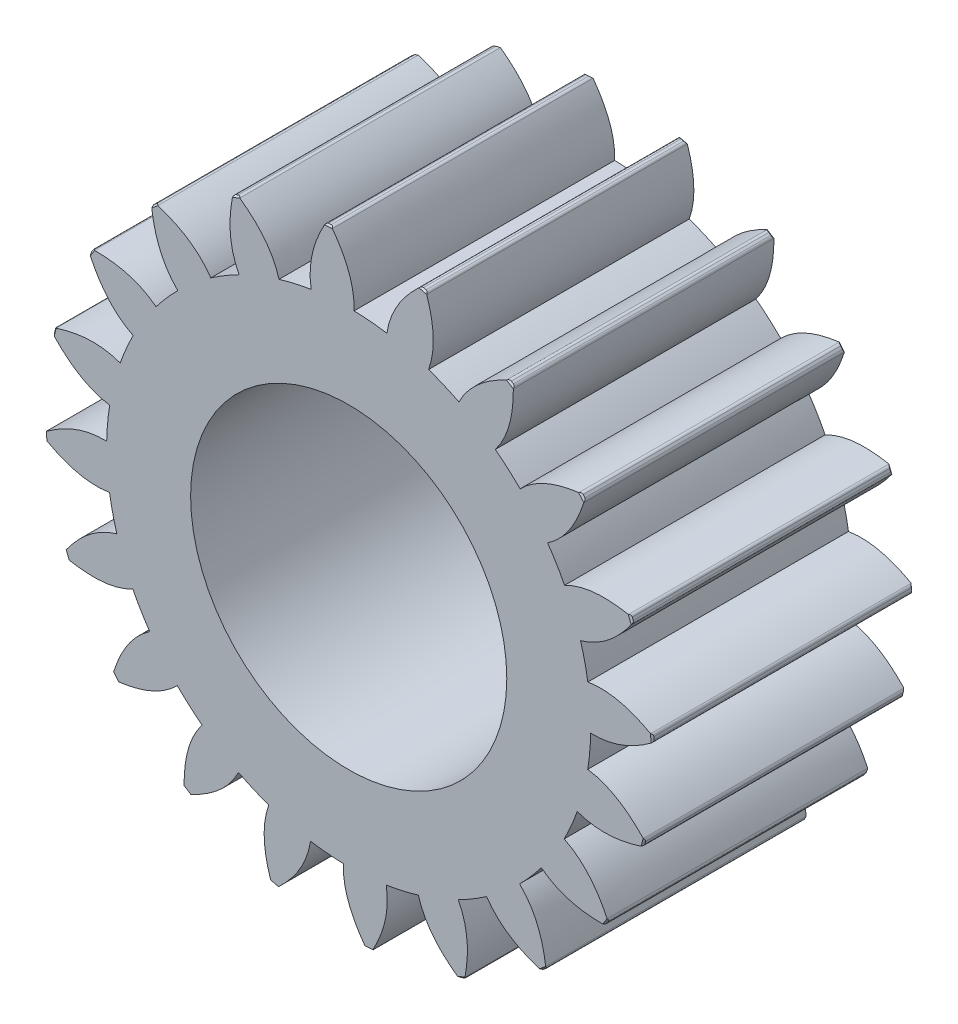
SolidWorks part; units mm, degrees
ref_plane "Front Plane" through (0, 0, 0) normal (0, 0, 1) x (1, 0, 0)
ref_plane "Top Plane" through (0, 0, 0) normal (0, 1, 0) x (1, 0, 0)
ref_plane "Right Plane" through (0, 0, 0) normal (1, 0, 0) x (0, 0, -1)
sketch "Sketch1" plane through (0, 0, 0) normal (0, 0, 1) x (1, 0, 0)
  line L0 (-4.8822, 32.0048) -> (-2.1352, 31.9521) construction
  line L1 (6.1058, 31.794) -> (16.3902, 27.9196) construction
  line L2 (16.3902, 27.9196) -> (24.7859, 20.8279) construction
  line L3 (24.7859, 20.8279) -> (30.3254, 11.3361) construction
  line L4 (6.1058, 31.794) -> (-4.687, 33.8667) construction
  line L5 (16.3902, 27.9196) -> (-2.565, 39.0472) construction
  line L6 (24.7859, 20.8279) -> (3.5752, 46.0693) construction
  line L7 (30.3254, 11.3361) -> (14.9328, 52.5132) construction
  line L8 (0, 0) -> (0.5872, 30.6194) construction
  line L9 (-4.8822, 32.0048) -> (-2.1352, 31.9521)
  line L10 (0, 0) -> (-2.1352, 31.9521) construction
  circle A1 centre (0, 0) radius 32.375
  circle A2 centre (0, 0) radius 30.625
  circle A3 centre (0, 0) radius 35 construction
  arc A4 (-1.5778, 38.4677) -> (-2.9487, 38.3869) centre (0, 0) ccw
  spline S0 degree 3 poles (-4.7486, 30.2546) (-4.8483, 30.8443) (-4.9361, 32.0654) (-4.6281, 34.862) (-3.7447, 36.9627) (-2.9487, 38.3869) knots -0.057438 -0.057438 -0.057438 -0.057438 0 0.062704 0.224889 0.224889 0.224889 0.224889
  spline S1 degree 3 poles (0.6808, 30.6174) (0.7012, 31.2152) (0.6257, 32.437) (-0.0517, 35.1678) (-1.2067, 37.1323) (-2.1851, 38.4379) knots -0.057438 -0.057438 -0.057438 -0.057438 0 0.062704 0.224889 0.224889 0.224889 0.224889
  spline S3 degree 3 poles (-2.6049, 38.9807) (-2.5916, 39.0029) (-2.5783, 39.025) (-2.565, 39.0472) knots 0.247636 0.247636 0.247636 0.247636 0.250208 0.250208 0.250208 0.250208
  dimension "D2" = 70
  dimension "D3" = 64.75
  dimension "D4" = 61.25
  dimension "D5" = 10.99
  dimension "D6" = 10.99
  dimension "D7" = 21.98
  dimension "D8" = 32.97
  dimension "D9" = 43.96
extrude "Boss-Extrude1" add sketch "Sketch1" along normal blind 32.97
chamfer "Chamfer1" distance 0.2 angle 45 2 edges at (-2.567, 38.4143, 0) (-2.567, 38.4143, 32.97)
fillet "Fillet1" radius 0.4 2 edges at (-2.1851, 38.4379, 16.485) (-2.9487, 38.3869, 16.485)
pattern_circular "CirPattern1" count 20 over 360 of "Fillet1", "Boss-Extrude1", "Chamfer1"
sketch "Sketch2" plane through (0, 0, 0) normal (0, 0, -1) x (-1, 0, 0)
  circle A0 centre (0, 0) radius 20
  dimension "D1" = 40
extrude "Cut-Extrude1" cut sketch "Sketch2" against normal through all
